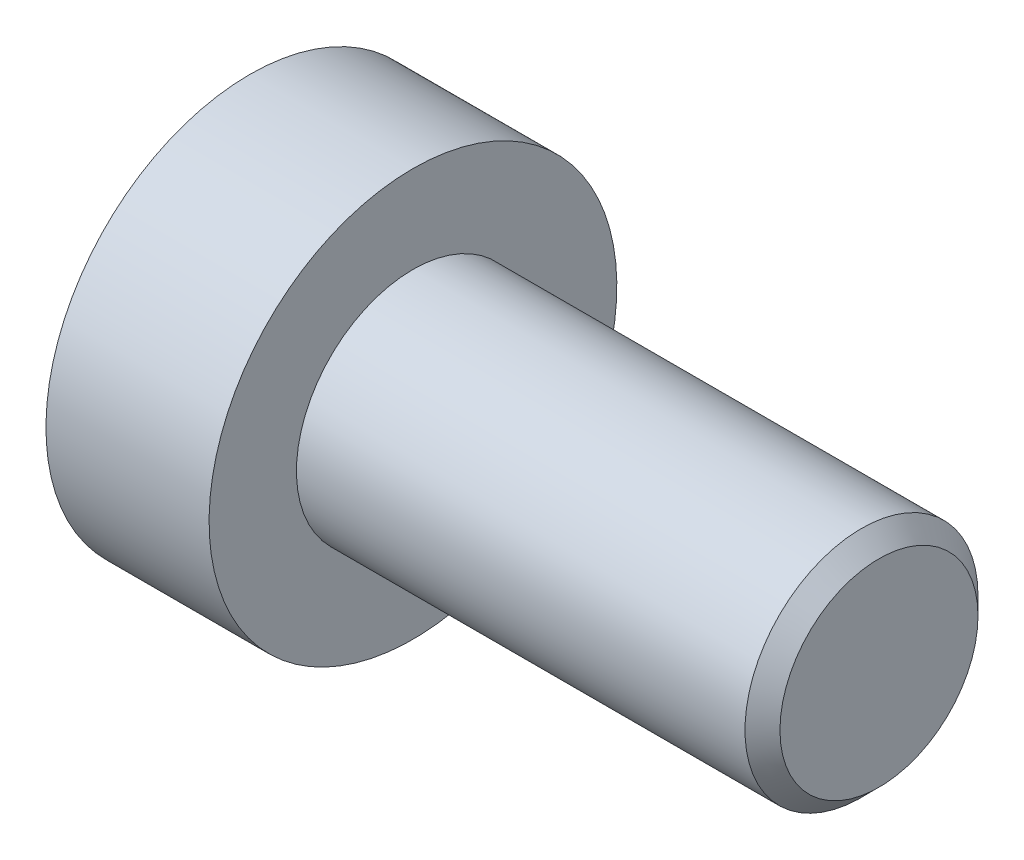
SolidWorks part; units mm, degrees
material "Plain Carbon Steel"
ref_plane "Front Plane" through (0, 0, 0) normal (0, 0, 1) x (1, 0, 0)
ref_plane "Top Plane" through (0, 0, 0) normal (0, 1, 0) x (1, 0, 0)
ref_plane "Right Plane" through (0, 0, 0) normal (1, 0, 0) x (0, 0, -1)
sketch "Sketch2" plane through (0, 0, 0) normal (1, 0, 0) x (0, 0, -1)
  circle A0 centre (0, 0) radius 2
  dimension "D1" = 4
extrude "Boss-Extrude1" add sketch "Sketch2" against normal blind 8
chamfer "Chamfer1" distance 0.3 angle 45 1 edges at (0, 0, -2)
sketch "Sketch6" plane through (0, 0, 0) normal (0, 0, 1) x (1, 0, 0)
  line L0 (-10.8, 0) -> (-10.8, 3.5)
  line L1 (-10.8, 0) -> (-8, 0)
  line L2 (-10.8, 3.5) -> (-8, 3.5)
  line L6 (-8, 3.5) -> (-8, 0)
  line L8 (-8, 0) -> (-14.6471, 0) construction
  line L10 (-8, 2) -> (-8, -2) construction
  dimension "D1" = 2.8
  dimension "D2" = 7
revolve "Revolve1" add sketch "Sketch6" angle 360 about L8
sketch "Sketch7" plane through (-10.8, 0, 0) normal (-1, 0, 0) x (0, 0, 1)
  line L1 (0, 1.4434) -> (-1.25, 0.7217)
  line L2 (-1.25, 0.7217) -> (-1.25, -0.7217)
  line L3 (-1.25, -0.7217) -> (0, -1.4434)
  line L4 (0, -1.4434) -> (1.25, -0.7217)
  line L5 (1.25, -0.7217) -> (1.25, 0.7217)
  line L6 (1.25, 0.7217) -> (0, 1.4434)
  circle A0 centre (0, 0) radius 1.25 construction
  dimension "D1" = 2.5
extrude "Cut-Extrude1" cut sketch "Sketch7" against normal blind 1.6
sketch "Sketch8" plane through (-10.8, 0, 0) normal (-1, 0, 0) x (0, 0, 1)
  circle A0 centre (0, 0) radius 1.4934
  dimension "D1" = 0.05
extrude "Cut-Extrude2" cut sketch "Sketch8" against normal blind 1 draft 45
